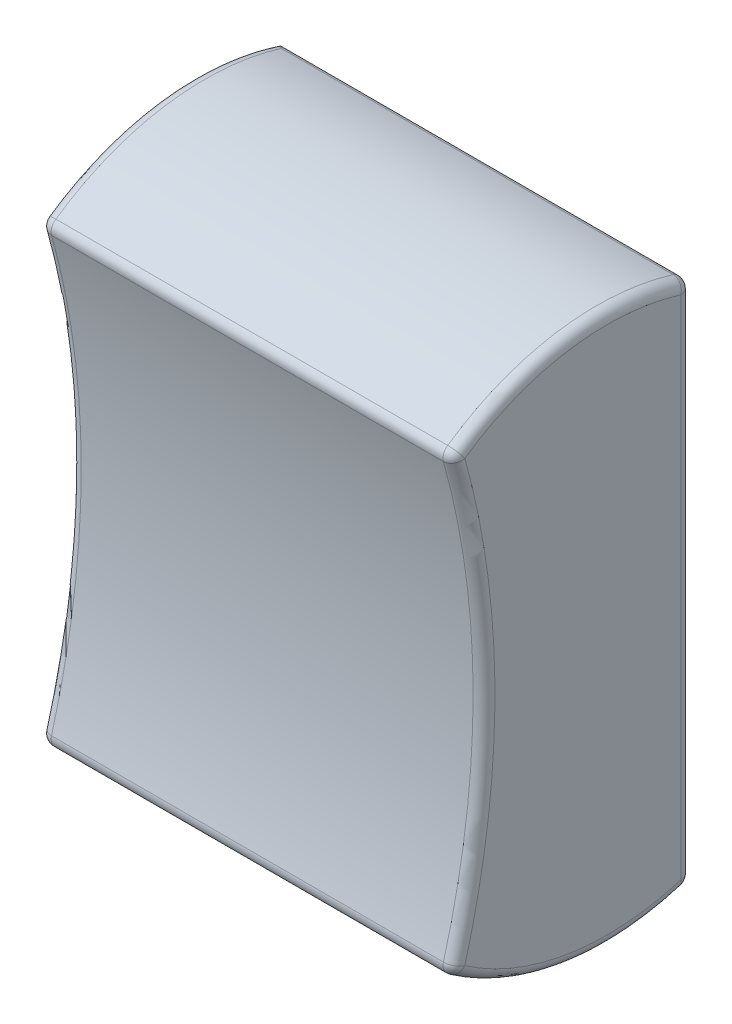
SolidWorks part; units mm, degrees
ref_plane "Front Plane" through (0, 0, 0) normal (0, 0, 1) x (1, 0, 0)
ref_plane "Top Plane" through (0, 0, 0) normal (0, 1, 0) x (1, 0, 0)
ref_plane "Right Plane" through (0, 0, 0) normal (1, 0, 0) x (0, 0, -1)
sketch "Sketch2" plane through (0, 0, 0) normal (1, 0, 0) x (0, 0, -1)
  line L0 (0, 12) -> (0, -12)
  arc A0 (-11, -10.29) -> (-11, 10.29) centre (-46.5403, 0) ccw
  arc A3 (-11, 10.29) -> (0, 12) centre (-3.867, 0.6401) cw
  arc A4 (-11, -10.29) -> (0, -12) centre (-3.867, -0.6401) ccw
  point P4 (0, 0)
  dimension "D2" = 12
  dimension "D3" = 37
  dimension "D1" = 20.58
  dimension "D4" = 24
  dimension "D5" = 11
extrude "Boss-Extrude2" add sketch "Sketch2" along normal mid plane 19
fillet "Fillet1" radius 0.5 11 edges at (0, -12, 0) (0, -10.29, 11) (-9.5, -12.4977, 5.7103) (9.5, -12.4977, 5.7103) (9.5, 0, 0) (0, 12, 0) (0, 10.29, 11) (9.5, 12.4977, 5.7103) (-9.5, 12.4977, 5.7103) (-9.5, 0, 9.5403) (9.5, 0, 9.5403)
